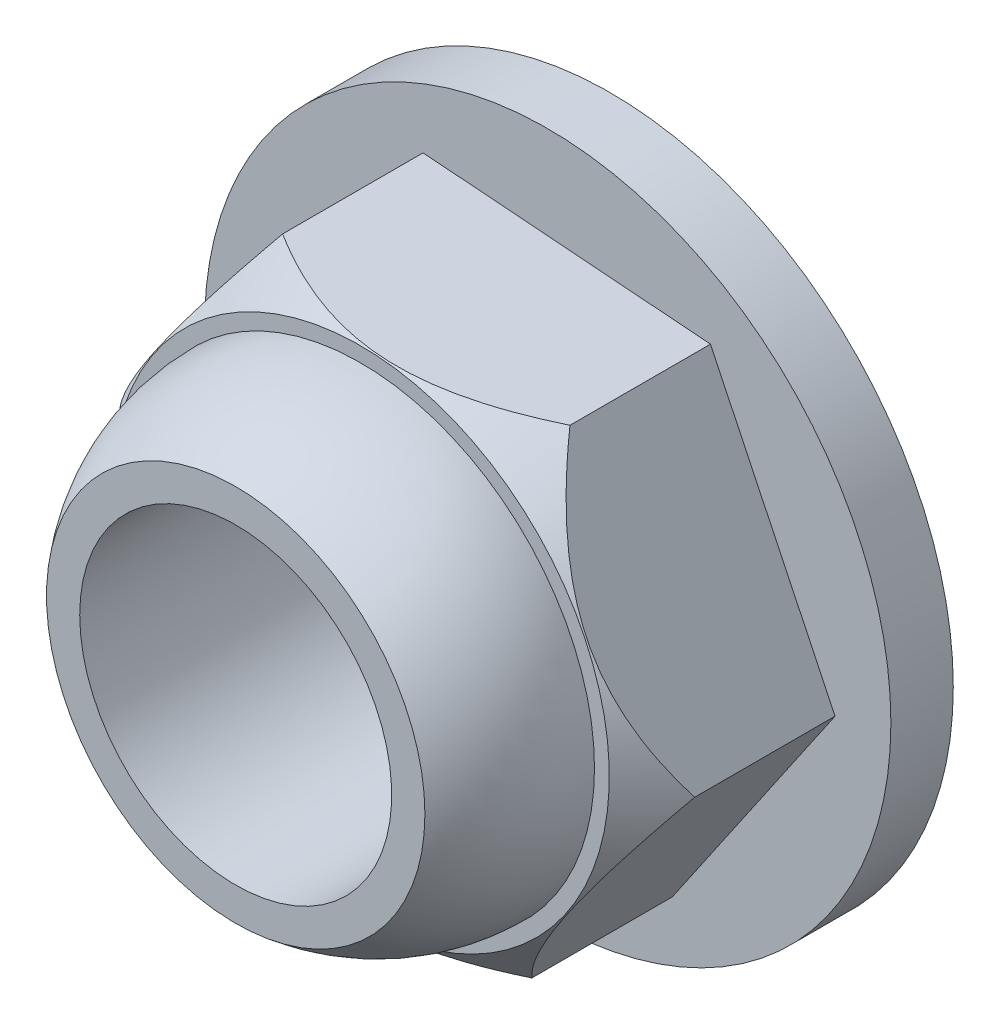
SolidWorks part; units mm, degrees
ref_plane "Спереди" through (0, 0, 0) normal (0, 0, 1) x (1, 0, 0)
ref_plane "Сверху" through (0, 0, 0) normal (0, 1, 0) x (1, 0, 0)
ref_plane "Справа" through (0, 0, 0) normal (1, 0, 0) x (0, 0, -1)
sketch "Эскиз1" plane through (0, 0, 0) normal (0, 0, 1) x (1, 0, 0)
  circle A0 centre (0, 0) radius 5.5
  dimension "D1" = 11
extrude "Бобышка-Вытянуть1" add sketch "Эскиз1" along normal blind 1
sketch "Эскиз3" plane through (0, 0, 1) normal (0, 0, 1) x (1, 0, 0)
  line L1 (2.6082, 3.8119) -> (-1.9971, 4.1647)
  line L2 (-1.9971, 4.1647) -> (-4.6053, 0.3528)
  line L3 (-4.6053, 0.3528) -> (-2.6082, -3.8119)
  line L4 (-2.6082, -3.8119) -> (1.9971, -4.1647)
  line L5 (1.9971, -4.1647) -> (4.6053, -0.3528)
  line L6 (4.6053, -0.3528) -> (2.6082, 3.8119)
  circle A0 centre (0, 0) radius 4 construction
  dimension "D1" = 8
extrude "Бобышка-Вытянуть2" add sketch "Эскиз3" along normal blind 3
ref_plane "Плоскость1" through (0, 0, 0) normal (-0.0764, -0.9971, 0) x (-0.9971, 0.0764, 0)
sketch "Эскиз5" plane through (0, 0, 0) normal (-0.0764, -0.9971, 0) x (-0.9971, 0.0764, 0)
  line L0 (0, 0) -> (0, -6.2015) construction
  line L10 (-4.6188, -3.2515) -> (-4.6188, -4)
  line L11 (-4.6188, -4) -> (-4.6188, -1) construction
  line L12 (-4.6188, -4) -> (-3.9876, -4)
  line L13 (-2.3094, -4) -> (-4.6188, -4) construction
  line L14 (-3.9876, -4) -> (-4.6188, -3.2515)
  point P7 (-4.6188, -3.2515)
  point P11 (-3.8877, -4)
  point P14 (0, 0)
  point P15 (-3.9876, -4)
revolve "Вырез-Повернуть3" cut sketch "Эскиз5" angle 360 about L0
sketch "Эскиз6" plane through (0, 0, 0) normal (1, 0, 0) x (0, 0, -1)
  line L0 (-0.9298, 0) -> (2.9208, 0) construction
  line L1 (-4, 3.9876) -> (-4, -3.9876) construction
  line L2 (-4, 0) -> (-4, 3.75)
  line L3 (-4, 0) -> (-6, 0)
  line L4 (-6, 0) -> (-6, 3.0322)
  arc A0 (-4, 3.75) -> (-6, 3.0322) centre (-4, 0.6048) ccw
  point P1 (-4, 0)
  dimension "D1" = 3.75
  dimension "D2" = 2
revolve "Повернуть1" add sketch "Эскиз6" angle 360 about L0
sketch "Эскиз8" plane through (0, 0, 6) normal (0, 0, 1) x (1, 0, 0)
  circle A0 centre (0, 0) radius 2
  dimension "D1" = 4
sketch "Эскиз9" plane through (0, 0, 0) normal (0, 0, -1) x (-1, 0, 0)
  circle A0 centre (0, 0) radius 2.5
  dimension "D1" = 5
extrude "Вырез-Вытянуть2" cut sketch "Эскиз9" against normal up to next
cosmetic thread "Условное изображение резьбы1" parameters "D1"=5, "D2"=6
chamfer "Фаска1" distance 0.3 angle 45 1 edges at (-2.5, 0, 0)
